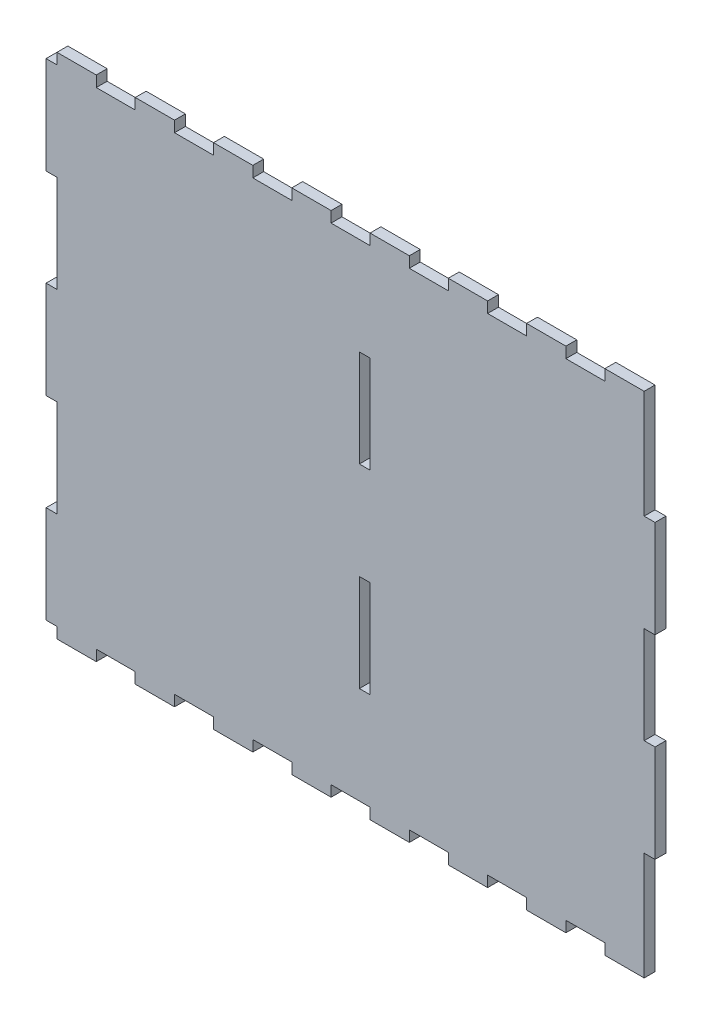
SolidWorks part; units mm, degrees
ref_plane "Front Plane" through (0, 0, 0) normal (0, 0, 1) x (1, 0, 0)
ref_plane "Top Plane" through (0, 0, 0) normal (0, 1, 0) x (1, 0, 0)
ref_plane "Right Plane" through (0, 0, 0) normal (1, 0, 0) x (0, 0, -1)
sketch "Sketch1" plane through (0, 0, 0) normal (0, 0, 1) x (1, 0, 0)
  line L0 (-200.4534, -13.9676) -> (-200.4534, -8.5676)
  line L1 (-239.3034, -13.9676) -> (52.0716, -13.9676)
  line L2 (-239.3034, -13.9676) -> (-239.3034, -255.2926)
  line L3 (-239.3034, -255.2926) -> (52.0716, -255.2926)
  line L4 (52.0716, -13.9676) -> (52.0716, -255.2926)
  line L5 (-239.3034, -13.9676) -> (-219.8784, -13.9676)
  line L6 (-239.3034, -13.9676) -> (-239.3034, -8.5676)
  line L7 (-239.3034, -8.5676) -> (-219.8784, -8.5676)
  line L8 (-219.8784, -13.9676) -> (-219.8784, -8.5676)
  line L9 (-200.4534, -8.5676) -> (-181.0284, -8.5676)
  line L10 (-181.0284, -13.9676) -> (-181.0284, -8.5676)
  line L11 (-161.6034, -13.9676) -> (-161.6034, -8.5676)
  line L12 (-161.6034, -8.5676) -> (-142.1784, -8.5676)
  line L13 (-142.1784, -13.9676) -> (-142.1784, -8.5676)
  line L14 (-122.7534, -13.9676) -> (-122.7534, -8.5676)
  line L15 (-122.7534, -8.5676) -> (-103.3284, -8.5676)
  line L16 (-103.3284, -13.9676) -> (-103.3284, -8.5676)
  line L17 (-83.9034, -13.9676) -> (-83.9034, -8.5676)
  line L18 (-83.9034, -8.5676) -> (-64.4784, -8.5676)
  line L19 (-64.4784, -13.9676) -> (-64.4784, -8.5676)
  line L20 (-45.0534, -13.9676) -> (-45.0534, -8.5676)
  line L21 (-45.0534, -8.5676) -> (-25.6284, -8.5676)
  line L22 (-25.6284, -13.9676) -> (-25.6284, -8.5676)
  line L23 (-6.2034, -13.9676) -> (-6.2034, -8.5676)
  line L24 (-6.2034, -8.5676) -> (13.2216, -8.5676)
  line L25 (13.2216, -13.9676) -> (13.2216, -8.5676)
  line L26 (32.6466, -13.9676) -> (32.6466, -8.5676)
  line L27 (32.6466, -8.5676) -> (52.0716, -8.5676)
  line L28 (52.0716, -13.9676) -> (52.0716, -8.5676)
  line L30 (-239.3034, -13.9676) -> (-244.7034, -13.9676)
  line L31 (-239.3034, -13.9676) -> (-239.3034, -62.2326)
  line L32 (-239.3034, -62.2326) -> (-244.7034, -62.2326)
  line L33 (-244.7034, -13.9676) -> (-244.7034, -62.2326)
  line L36 (-239.3034, -207.0276) -> (-244.7034, -207.0276)
  line L37 (-244.7034, -207.0276) -> (-244.7034, -255.2926)
  line L38 (-239.3034, -255.2926) -> (-244.7034, -255.2926)
  line L39 (52.0716, -158.7626) -> (57.4716, -158.7626)
  line L40 (52.0716, -62.2326) -> (57.4716, -62.2326)
  line L41 (52.0716, -62.2326) -> (52.0716, -110.4976)
  line L42 (52.0716, -110.4976) -> (57.4716, -110.4976)
  line L43 (57.4716, -62.2326) -> (57.4716, -110.4976)
  line L44 (57.4716, -158.7626) -> (57.4716, -207.0276)
  line L45 (52.0716, -207.0276) -> (57.4716, -207.0276)
  line L46 (-93.6159, -13.9676) -> (-93.6159, -94.2326) construction
  line L47 (-93.6159, -94.2326) -> (-93.6159, -255.2926) construction
  line L48 (-83.8784, -62.2326) -> (-89.2784, -62.2326)
  line L49 (-83.8784, -62.2326) -> (-83.8784, -110.4976)
  line L50 (-83.8784, -110.4976) -> (-89.2784, -110.4976)
  line L51 (-89.2784, -62.2326) -> (-89.2784, -110.4976)
  line L52 (-83.8784, -158.7626) -> (-89.2784, -158.7626)
  line L53 (-83.8784, -158.7626) -> (-83.8784, -207.0276)
  line L54 (-83.8784, -207.0276) -> (-89.2784, -207.0276)
  line L55 (-89.2784, -158.7626) -> (-89.2784, -207.0276)
  line L56 (52.0716, -134.6301) -> (-244.7034, -134.6301) construction
  line L57 (52.0716, -255.2926) -> (52.0716, -260.6926)
  line L58 (32.6466, -260.6926) -> (52.0716, -260.6926)
  line L59 (32.6466, -255.2926) -> (32.6466, -260.6926)
  line L60 (13.2216, -255.2926) -> (13.2216, -260.6926)
  line L61 (-6.2034, -260.6926) -> (13.2216, -260.6926)
  line L62 (-6.2034, -255.2926) -> (-6.2034, -260.6926)
  line L63 (-25.6284, -255.2926) -> (-25.6284, -260.6926)
  line L64 (-45.0534, -260.6926) -> (-25.6284, -260.6926)
  line L65 (-45.0534, -255.2926) -> (-45.0534, -260.6926)
  line L66 (-64.4784, -255.2926) -> (-64.4784, -260.6926)
  line L67 (-83.9034, -260.6926) -> (-64.4784, -260.6926)
  line L68 (-83.9034, -255.2926) -> (-83.9034, -260.6926)
  line L69 (-103.3284, -255.2926) -> (-103.3284, -260.6926)
  line L70 (-122.7534, -260.6926) -> (-103.3284, -260.6926)
  line L71 (-122.7534, -255.2926) -> (-122.7534, -260.6926)
  line L72 (-142.1784, -255.2926) -> (-142.1784, -260.6926)
  line L73 (-161.6034, -260.6926) -> (-142.1784, -260.6926)
  line L74 (-161.6034, -255.2926) -> (-161.6034, -260.6926)
  line L75 (-181.0284, -255.2926) -> (-181.0284, -260.6926)
  line L76 (-200.4534, -260.6926) -> (-181.0284, -260.6926)
  line L77 (-200.4534, -255.2926) -> (-200.4534, -260.6926)
  line L78 (-219.8784, -255.2926) -> (-219.8784, -260.6926)
  line L79 (-239.3034, -255.2926) -> (-239.3034, -260.6926)
  line L80 (-239.3034, -260.6926) -> (-219.8784, -260.6926)
  line L81 (-239.3034, -110.4976) -> (-244.7034, -110.4976)
  line L82 (-239.3034, -110.4976) -> (-239.3034, -158.7626)
  line L83 (-239.3034, -158.7626) -> (-244.7034, -158.7626)
  line L84 (-244.7034, -110.4976) -> (-244.7034, -158.7626)
  point P63 (-87.528, -223.2926)
  point P66 (-77.0574, -159.2926)
  point P98 (-81.6297, -159.2926)
  dimension "D2" = 48.265
  dimension "D3" = 19.425
  dimension "D4" = 5.4
  dimension "D6" = 19.425
  dimension "D7" = 5.4
  dimension "D10" = 48.265
  dimension "D11" = 48.265
  dimension "D12" = 5.4
  dimension "D13" = 5.4
  dimension "D14" = 48.265
  dimension "D15" = 5.4
  dimension "D16" = 48.265
  dimension "D17" = 48.265
  dimension "D18" = 48.265
  dimension "D5" = 291.375
  dimension "D8" = 48.265
  dimension "D19" = 5.4
  dimension "D20" = 48.265
  dimension "D21" = 241.325
  dimension "D22" = 5.4
  dimension "D23" = 4.3375
  dimension "D24" = 4.3375
  dimension "D25" = 48.265
  dimension "D9" = 2
extrude "Boss-Extrude1" add sketch "Sketch1" along normal blind 5.4
sketch "Sketch2" plane through (0, 0, 5.4) normal (0, 0, 1) x (1, 0, 0)
  line L11 (-89.2377, -110.4569) -> (-83.919, -110.4569)
  line L12 (-83.919, -110.4569) -> (-83.919, -62.2732)
  line L13 (-89.2377, -62.2732) -> (-89.2377, -110.4569)
  line L14 (-83.919, -62.2732) -> (-89.2377, -62.2732)
  line L15 (-89.2377, -110.4569) -> (-83.919, -110.4569)
  line L16 (-83.919, -110.4569) -> (-83.919, -62.2732)
  line L17 (-89.2377, -62.2732) -> (-89.2377, -110.4569)
  line L18 (-83.919, -62.2732) -> (-89.2377, -62.2732)
  line L29 (-89.2377, -206.9869) -> (-83.919, -206.9869)
  line L30 (-83.919, -206.9869) -> (-83.919, -158.8032)
  line L31 (-89.2377, -158.8032) -> (-89.2377, -206.9869)
  line L32 (-83.919, -158.8032) -> (-89.2377, -158.8032)
  line L33 (-89.2377, -206.9869) -> (-83.919, -206.9869)
  line L34 (-83.919, -206.9869) -> (-83.919, -158.8032)
  line L35 (-89.2377, -158.8032) -> (-89.2377, -206.9869)
  line L36 (-83.919, -158.8032) -> (-89.2377, -158.8032)
  line L160 (-239.344, -8.5269) -> (-239.344, -13.9269)
  line L161 (-239.344, -13.9269) -> (-244.744, -13.9269)
  line L162 (-244.744, -13.9269) -> (-244.744, -62.2732)
  line L163 (-244.744, -62.2732) -> (-239.344, -62.2732)
  line L164 (-239.344, -62.2732) -> (-239.344, -110.4569)
  line L165 (-239.344, -110.4569) -> (-244.744, -110.4569)
  line L166 (-244.744, -110.4569) -> (-244.744, -158.8032)
  line L167 (-244.744, -158.8032) -> (-239.344, -158.8032)
  line L168 (-239.344, -158.8032) -> (-239.344, -206.9869)
  line L169 (-239.344, -206.9869) -> (-244.744, -206.9869)
  line L170 (-244.744, -206.9869) -> (-244.744, -255.3332)
  line L171 (-244.744, -255.3332) -> (-239.344, -255.3332)
  line L172 (-239.344, -255.3332) -> (-239.344, -260.7332)
  line L173 (-239.344, -260.7332) -> (-219.8377, -260.7332)
  line L174 (-219.8377, -260.7332) -> (-219.8377, -255.3332)
  line L175 (-219.8377, -255.3332) -> (-200.494, -255.3332)
  line L176 (-200.494, -255.3332) -> (-200.494, -260.7332)
  line L177 (-200.494, -260.7332) -> (-180.9877, -260.7332)
  line L178 (-180.9877, -260.7332) -> (-180.9877, -255.3332)
  line L179 (-180.9877, -255.3332) -> (-161.644, -255.3332)
  line L180 (-161.644, -255.3332) -> (-161.644, -260.7332)
  line L181 (-161.644, -260.7332) -> (-142.1377, -260.7332)
  line L182 (-142.1377, -260.7332) -> (-142.1377, -255.3332)
  line L183 (-142.1377, -255.3332) -> (-122.794, -255.3332)
  line L184 (-122.794, -255.3332) -> (-122.794, -260.7332)
  line L185 (-122.794, -260.7332) -> (-103.2877, -260.7332)
  line L186 (-103.2877, -260.7332) -> (-103.2877, -255.3332)
  line L187 (-103.2877, -255.3332) -> (-83.944, -255.3332)
  line L188 (-83.944, -255.3332) -> (-83.944, -260.7332)
  line L189 (-83.944, -260.7332) -> (-64.4377, -260.7332)
  line L190 (-64.4377, -260.7332) -> (-64.4377, -255.3332)
  line L191 (-64.4377, -255.3332) -> (-45.094, -255.3332)
  line L192 (-45.094, -255.3332) -> (-45.094, -260.7332)
  line L193 (-45.094, -260.7332) -> (-25.5877, -260.7332)
  line L194 (-25.5877, -260.7332) -> (-25.5877, -255.3332)
  line L195 (-25.5877, -255.3332) -> (-6.244, -255.3332)
  line L196 (-6.244, -255.3332) -> (-6.244, -260.7332)
  line L197 (-6.244, -260.7332) -> (13.2623, -260.7332)
  line L198 (13.2623, -260.7332) -> (13.2623, -255.3332)
  line L199 (13.2623, -255.3332) -> (32.606, -255.3332)
  line L200 (32.606, -255.3332) -> (32.606, -260.7332)
  line L201 (32.606, -260.7332) -> (52.1123, -260.7332)
  line L202 (52.1123, -260.7332) -> (52.1123, -207.0682)
  line L203 (52.1123, -207.0682) -> (57.5123, -207.0682)
  line L204 (57.5123, -207.0682) -> (57.5123, -158.7219)
  line L205 (57.5123, -158.7219) -> (52.1123, -158.7219)
  line L206 (52.1123, -158.7219) -> (52.1123, -110.5382)
  line L207 (52.1123, -110.5382) -> (57.5123, -110.5382)
  line L208 (57.5123, -110.5382) -> (57.5123, -62.1919)
  line L209 (57.5123, -62.1919) -> (52.1123, -62.1919)
  line L210 (52.1123, -62.1919) -> (52.1123, -8.5269)
  line L211 (52.1123, -8.5269) -> (32.606, -8.5269)
  line L212 (32.606, -8.5269) -> (32.606, -13.9269)
  line L213 (32.606, -13.9269) -> (13.2623, -13.9269)
  line L214 (13.2623, -13.9269) -> (13.2623, -8.5269)
  line L215 (13.2623, -8.5269) -> (-6.244, -8.5269)
  line L216 (-6.244, -8.5269) -> (-6.244, -13.9269)
  line L217 (-6.244, -13.9269) -> (-25.5877, -13.9269)
  line L218 (-25.5877, -13.9269) -> (-25.5877, -8.5269)
  line L219 (-25.5877, -8.5269) -> (-45.094, -8.5269)
  line L220 (-45.094, -8.5269) -> (-45.094, -13.9269)
  line L221 (-45.094, -13.9269) -> (-64.4377, -13.9269)
  line L222 (-64.4377, -13.9269) -> (-64.4377, -8.5269)
  line L223 (-64.4377, -8.5269) -> (-83.944, -8.5269)
  line L224 (-83.944, -8.5269) -> (-83.944, -13.9269)
  line L225 (-83.944, -13.9269) -> (-103.2877, -13.9269)
  line L226 (-103.2877, -13.9269) -> (-103.2877, -8.5269)
  line L227 (-103.2877, -8.5269) -> (-122.794, -8.5269)
  line L228 (-122.794, -8.5269) -> (-122.794, -13.9269)
  line L229 (-122.794, -13.9269) -> (-142.1377, -13.9269)
  line L230 (-142.1377, -13.9269) -> (-142.1377, -8.5269)
  line L231 (-142.1377, -8.5269) -> (-161.644, -8.5269)
  line L232 (-161.644, -8.5269) -> (-161.644, -13.9269)
  line L233 (-161.644, -13.9269) -> (-180.9877, -13.9269)
  line L234 (-180.9877, -13.9269) -> (-180.9877, -8.5269)
  line L235 (-180.9877, -8.5269) -> (-200.494, -8.5269)
  line L236 (-200.494, -8.5269) -> (-200.494, -13.9269)
  line L237 (-200.494, -13.9269) -> (-219.8377, -13.9269)
  line L238 (-219.8377, -13.9269) -> (-219.8377, -8.5269)
  line L239 (-219.8377, -8.5269) -> (-239.344, -8.5269)
  line L240 (-239.344, -8.5269) -> (-239.344, -13.9269)
  line L241 (-239.344, -13.9269) -> (-244.744, -13.9269)
  line L242 (-244.744, -13.9269) -> (-244.744, -62.2732)
  line L243 (-244.744, -62.2732) -> (-239.344, -62.2732)
  line L244 (-239.344, -62.2732) -> (-239.344, -110.4569)
  line L245 (-239.344, -110.4569) -> (-244.744, -110.4569)
  line L246 (-244.744, -110.4569) -> (-244.744, -158.8032)
  line L247 (-244.744, -158.8032) -> (-239.344, -158.8032)
  line L248 (-239.344, -158.8032) -> (-239.344, -206.9869)
  line L249 (-239.344, -206.9869) -> (-244.744, -206.9869)
  line L250 (-244.744, -206.9869) -> (-244.744, -255.3332)
  line L251 (-244.744, -255.3332) -> (-239.344, -255.3332)
  line L252 (-239.344, -255.3332) -> (-239.344, -260.7332)
  line L253 (-239.344, -260.7332) -> (-219.8377, -260.7332)
  line L254 (-219.8377, -260.7332) -> (-219.8377, -255.3332)
  line L255 (-219.8377, -255.3332) -> (-200.494, -255.3332)
  line L256 (-200.494, -255.3332) -> (-200.494, -260.7332)
  line L257 (-200.494, -260.7332) -> (-180.9877, -260.7332)
  line L258 (-180.9877, -260.7332) -> (-180.9877, -255.3332)
  line L259 (-180.9877, -255.3332) -> (-161.644, -255.3332)
  line L260 (-161.644, -255.3332) -> (-161.644, -260.7332)
  line L261 (-161.644, -260.7332) -> (-142.1377, -260.7332)
  line L262 (-142.1377, -260.7332) -> (-142.1377, -255.3332)
  line L263 (-142.1377, -255.3332) -> (-122.794, -255.3332)
  line L264 (-122.794, -255.3332) -> (-122.794, -260.7332)
  line L265 (-122.794, -260.7332) -> (-103.2877, -260.7332)
  line L266 (-103.2877, -260.7332) -> (-103.2877, -255.3332)
  line L267 (-103.2877, -255.3332) -> (-83.944, -255.3332)
  line L268 (-83.944, -255.3332) -> (-83.944, -260.7332)
  line L269 (-83.944, -260.7332) -> (-64.4377, -260.7332)
  line L270 (-64.4377, -260.7332) -> (-64.4377, -255.3332)
  line L271 (-64.4377, -255.3332) -> (-45.094, -255.3332)
  line L272 (-45.094, -255.3332) -> (-45.094, -260.7332)
  line L273 (-45.094, -260.7332) -> (-25.5877, -260.7332)
  line L274 (-25.5877, -260.7332) -> (-25.5877, -255.3332)
  line L275 (-25.5877, -255.3332) -> (-6.244, -255.3332)
  line L276 (-6.244, -255.3332) -> (-6.244, -260.7332)
  line L277 (-6.244, -260.7332) -> (13.2623, -260.7332)
  line L278 (13.2623, -260.7332) -> (13.2623, -255.3332)
  line L279 (13.2623, -255.3332) -> (32.606, -255.3332)
  line L280 (32.606, -255.3332) -> (32.606, -260.7332)
  line L281 (32.606, -260.7332) -> (52.1123, -260.7332)
  line L282 (52.1123, -260.7332) -> (52.1123, -207.0682)
  line L283 (52.1123, -207.0682) -> (57.5123, -207.0682)
  line L284 (57.5123, -207.0682) -> (57.5123, -158.7219)
  line L285 (57.5123, -158.7219) -> (52.1123, -158.7219)
  line L286 (52.1123, -158.7219) -> (52.1123, -110.5382)
  line L287 (52.1123, -110.5382) -> (57.5123, -110.5382)
  line L288 (57.5123, -110.5382) -> (57.5123, -62.1919)
  line L289 (57.5123, -62.1919) -> (52.1123, -62.1919)
  line L290 (52.1123, -62.1919) -> (52.1123, -8.5269)
  line L291 (52.1123, -8.5269) -> (32.606, -8.5269)
  line L292 (32.606, -8.5269) -> (32.606, -13.9269)
  line L293 (32.606, -13.9269) -> (13.2623, -13.9269)
  line L294 (13.2623, -13.9269) -> (13.2623, -8.5269)
  line L295 (13.2623, -8.5269) -> (-6.244, -8.5269)
  line L296 (-6.244, -8.5269) -> (-6.244, -13.9269)
  line L297 (-6.244, -13.9269) -> (-25.5877, -13.9269)
  line L298 (-25.5877, -13.9269) -> (-25.5877, -8.5269)
  line L299 (-25.5877, -8.5269) -> (-45.094, -8.5269)
  line L300 (-45.094, -8.5269) -> (-45.094, -13.9269)
  line L301 (-45.094, -13.9269) -> (-64.4377, -13.9269)
  line L302 (-64.4377, -13.9269) -> (-64.4377, -8.5269)
  line L303 (-64.4377, -8.5269) -> (-83.944, -8.5269)
  line L304 (-83.944, -8.5269) -> (-83.944, -13.9269)
  line L305 (-83.944, -13.9269) -> (-103.2877, -13.9269)
  line L306 (-103.2877, -13.9269) -> (-103.2877, -8.5269)
  line L307 (-103.2877, -8.5269) -> (-122.794, -8.5269)
  line L308 (-122.794, -8.5269) -> (-122.794, -13.9269)
  line L309 (-122.794, -13.9269) -> (-142.1377, -13.9269)
  line L310 (-142.1377, -13.9269) -> (-142.1377, -8.5269)
  line L311 (-142.1377, -8.5269) -> (-161.644, -8.5269)
  line L312 (-161.644, -8.5269) -> (-161.644, -13.9269)
  line L313 (-161.644, -13.9269) -> (-180.9877, -13.9269)
  line L314 (-180.9877, -13.9269) -> (-180.9877, -8.5269)
  line L315 (-180.9877, -8.5269) -> (-200.494, -8.5269)
  line L316 (-200.494, -8.5269) -> (-200.494, -13.9269)
  line L317 (-200.494, -13.9269) -> (-219.8377, -13.9269)
  line L318 (-219.8377, -13.9269) -> (-219.8377, -8.5269)
  line L319 (-219.8377, -8.5269) -> (-239.344, -8.5269)
  dimension "D1" = 0.0406
  dimension "D2" = 0.0406
  dimension "D3" = 0.0406
extrude "Boss-Extrude2" add sketch "Sketch2" against normal up to surface (5.4 mm away) up to face at (-101.0353, -134.6301, 0)
equation "\"Structure Height\"= 26"
